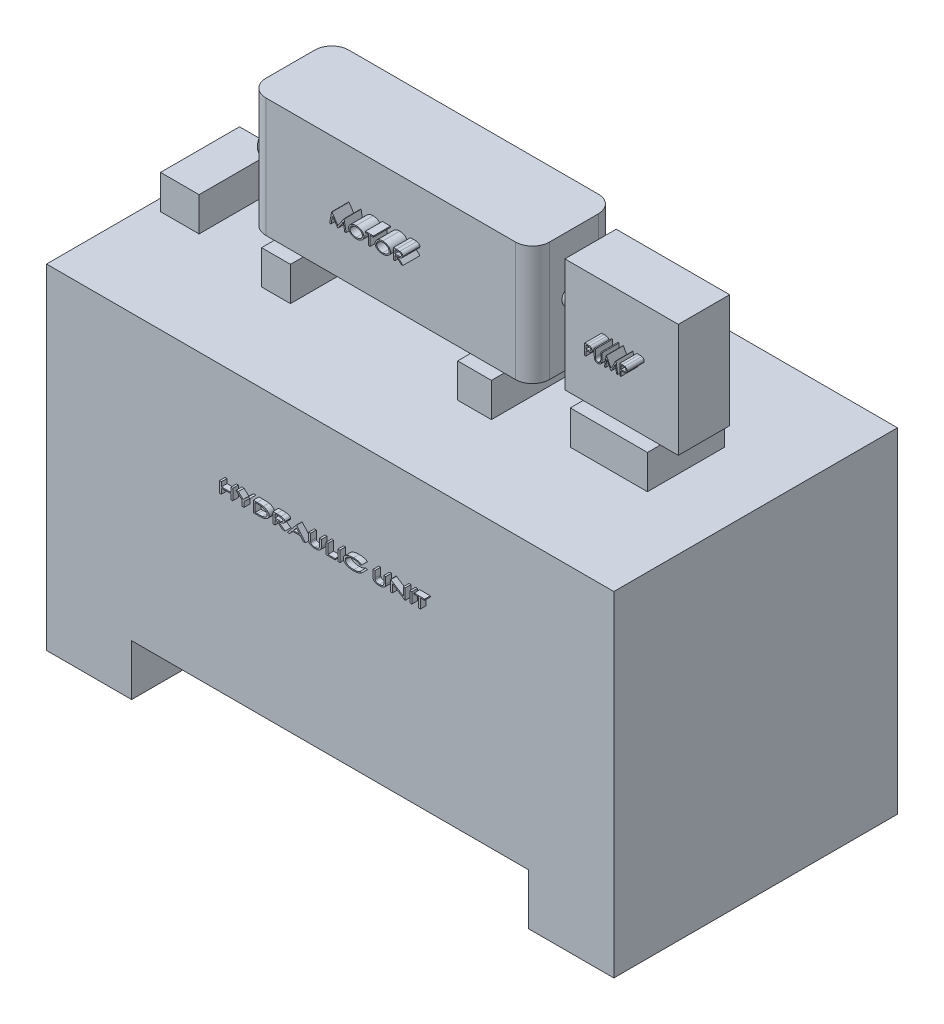
SolidWorks part; units mm, degrees
ref_plane "Front Plane" through (0, 0, 0) normal (0, 0, 1) x (1, 0, 0)
ref_plane "Top Plane" through (0, 0, 0) normal (0, 1, 0) x (1, 0, 0)
ref_plane "Right Plane" through (0, 0, 0) normal (1, 0, 0) x (0, 0, -1)
sketch "Sketch2" plane through (0, 0, 0) normal (0, 1, 0) x (1, 0, 0)
  line L1 (-500, -250) -> (500, -250)
  line L2 (-500, -250) -> (-500, 250)
  line L3 (-500, 250) -> (500, 250)
  line L4 (500, -250) -> (500, 250)
  line L5 (-500, -250) -> (500, 250) construction
  line L6 (-500, 250) -> (500, -250) construction
  point P0 (0, 0)
  dimension "D1" = 1000
  dimension "D2" = 500
extrude "Boss-Extrude1" add sketch "Sketch2" along normal blind 500
sketch "Sketch3" plane through (0, 0, 0) normal (0, -1, 0) x (1, 0, 0)
  line L0 (500, -250) -> (-500, -250) construction
  line L1 (-500, 250) -> (-350, 250)
  line L2 (-500, 250) -> (-500, -250)
  line L3 (-500, -250) -> (-350, -250)
  line L4 (-350, 250) -> (-350, -250)
  line L6 (500, 250) -> (350, 250)
  line L7 (500, 250) -> (500, -250)
  line L8 (500, -250) -> (350, -250)
  line L9 (350, 250) -> (350, -250)
  dimension "D1" = 150
  dimension "D2" = 150
extrude "Boss-Extrude2" add sketch "Sketch3" along normal blind 90
sketch "Sketch4" plane through (0, 500, 0) normal (0, 1, 0) x (1, 0, 0)
  line L1 (241.2914, -68.015) -> (377.3214, -68.015)
  line L2 (241.2914, -68.015) -> (241.2914, 68.015)
  line L3 (241.2914, 68.015) -> (377.3214, 68.015)
  line L4 (377.3214, -68.015) -> (377.3214, 68.015)
  line L5 (241.2914, -68.015) -> (377.3214, 68.015) construction
  line L6 (241.2914, 68.015) -> (377.3214, -68.015) construction
  point P0 (309.3064, 0)
extrude "Boss-Extrude3" add sketch "Sketch4" along normal blind 60
sketch "Sketch5" plane through (0, 560, 0) normal (0, 1, 0) x (1, 0, 0)
  line L5 (208.9413, -45.2588) -> (408.9475, -45.2588)
  line L6 (208.9413, -45.2588) -> (208.9413, 45.2588)
  line L7 (208.9413, 45.2588) -> (408.9475, 45.2588)
  line L8 (408.9475, -45.2588) -> (408.9475, 45.2588)
  line L9 (208.9413, -45.2588) -> (408.9475, 45.2588) construction
  line L10 (208.9413, 45.2588) -> (408.9475, -45.2588) construction
  point P0 (308.9444, 0)
extrude "Boss-Extrude4" add sketch "Sketch5" along normal blind 200
sketch "Sketch6" plane through (0, 500, 0) normal (0, 1, 0) x (1, 0, 0)
  line L1 (70.2841, -95.5153) -> (129.7159, -95.5153)
  line L2 (70.2841, -95.5153) -> (70.2841, 95.5153)
  line L3 (70.2841, 95.5153) -> (129.7159, 95.5153)
  line L4 (129.7159, -95.5153) -> (129.7159, 95.5153)
  line L5 (70.2841, -95.5153) -> (129.7159, 95.5153) construction
  line L6 (70.2841, 95.5153) -> (129.7159, -95.5153) construction
  line L7 (-275.4707, -95.5153) -> (-224.5293, -95.5153)
  line L8 (-275.4707, -95.5153) -> (-275.4707, 95.5153)
  line L9 (-275.4707, 95.5153) -> (-224.5293, 95.5153)
  line L10 (-224.5293, -95.5153) -> (-224.5293, 95.5153)
  line L11 (-275.4707, -95.5153) -> (-224.5293, 95.5153) construction
  line L12 (-275.4707, 95.5153) -> (-224.5293, -95.5153) construction
  point P0 (100, 0)
  point P5 (-250, 0)
  dimension "D1" = 350
  dimension "D2" = 250
extrude "Boss-Extrude5" add sketch "Sketch6" along normal blind 60
sketch "Sketch7" plane through (0, 560, 0) normal (0, 1, 0) x (1, 0, 0)
  line L0 (129.7159, -95.5153) -> (129.7159, 95.5153) construction
  line L1 (-290.2841, -73.0519) -> (149.7159, -73.0519)
  line L2 (-320.2841, -43.0519) -> (-320.2841, 43.0519)
  line L3 (-290.2841, 73.0519) -> (149.7159, 73.0519)
  line L4 (179.7159, -43.0519) -> (179.7159, 43.0519)
  line L5 (-320.2841, -73.0519) -> (179.7159, 73.0519) construction
  line L6 (-320.2841, 73.0519) -> (179.7159, -73.0519) construction
  arc A0 (149.7159, 73.0519) -> (179.7159, 43.0519) centre (149.7159, 43.0519) cw
  arc A1 (149.7159, -73.0519) -> (179.7159, -43.0519) centre (149.7159, -43.0519) ccw
  arc A2 (-290.2841, -73.0519) -> (-320.2841, -43.0519) centre (-290.2841, -43.0519) cw
  arc A3 (-320.2841, 43.0519) -> (-290.2841, 73.0519) centre (-290.2841, 43.0519) cw
  point P0 (-70.2841, 0)
  dimension "D3" = 30
  dimension "D1" = 200
  dimension "D2" = 250
extrude "Boss-Extrude6" add sketch "Sketch7" along normal blind 210
sketch "Sketch8" plane through (179.7159, 0, 0) normal (1, 0, 0) x (0, 0, -1)
  line L0 (-43.0519, 560) -> (43.0519, 560) construction
  circle A0 centre (-4.6059, 670) radius 16.5
  dimension "D1" = 33
  dimension "D2" = 110
extrude "Boss-Extrude7" add sketch "Sketch8" along normal blind 30
sketch "Sketch12" plane through (0, 500, 0) normal (0, 1, 0) x (1, 0, 0)
  line L0 (-275.4707, 95.5153) -> (-275.4707, -95.5153) construction
  line L1 (-479.4783, -69.6344) -> (-411.4632, -69.6344)
  line L2 (-479.4783, -69.6344) -> (-479.4783, 69.6344)
  line L3 (-479.4783, 69.6344) -> (-411.4632, 69.6344)
  line L4 (-411.4632, -69.6344) -> (-411.4632, 69.6344)
  line L5 (-479.4783, -69.6344) -> (-411.4632, 69.6344) construction
  line L6 (-479.4783, 69.6344) -> (-411.4632, -69.6344) construction
  point P0 (-445.4707, 0)
  dimension "D1" = 170
extrude "Boss-Extrude8" add sketch "Sketch12" along normal blind 60
sketch "Sketch17" plane through (0, 0, 250) normal (0, 0, 1) x (1, 0, 0)
  line L0 (-500, 312.6916) -> (500, 312.6916) construction
  line L1 (-500, 500) -> (-500, -90) construction
  line L2 (500, 500) -> (500, -90) construction
  text T0 "                        HYDRAULIC UNIT" font "Century Gothic" height in points 72
sketch "Sketch18" plane through (0, 0, 73.0519) normal (0, 0, 1) x (1, 0, 0)
  line L0 (-290.2841, 665) -> (149.7159, 665) construction
  line L1 (-290.2841, 770) -> (-290.2841, 560) construction
  line L2 (149.7159, 770) -> (149.7159, 560) construction
  text T0 "              MOTOR" font "Century Gothic" height in points 72
extrude "Boss-Extrude12" add sketch "Sketch18" along normal blind 30
sketch "Sketch20" plane through (0, 0, 45.2588) normal (0, 0, 1) x (1, 0, 0)
  line L0 (208.9413, 660) -> (419.6245, 660) construction
  line L1 (208.9413, 760) -> (208.9413, 560) construction
  text T0 "        PUMP" font "Century Gothic" height in points 72
extrude "Boss-Extrude14" add sketch "Sketch20" along normal blind 30
extrude "Boss-Extrude15" add sketch "Sketch17" along normal blind 10
sketch "Sketch21" plane through (-320.2841, 0, 0) normal (-1, 0, 0) x (0, 0, 1)
  line L0 (-43.0519, 560) -> (43.0519, 560) construction
  circle A0 centre (0, 640) radius 25
  dimension "D1" = 50
  dimension "D2" = 80
extrude "Boss-Extrude16" add sketch "Sketch21" along normal blind 33
